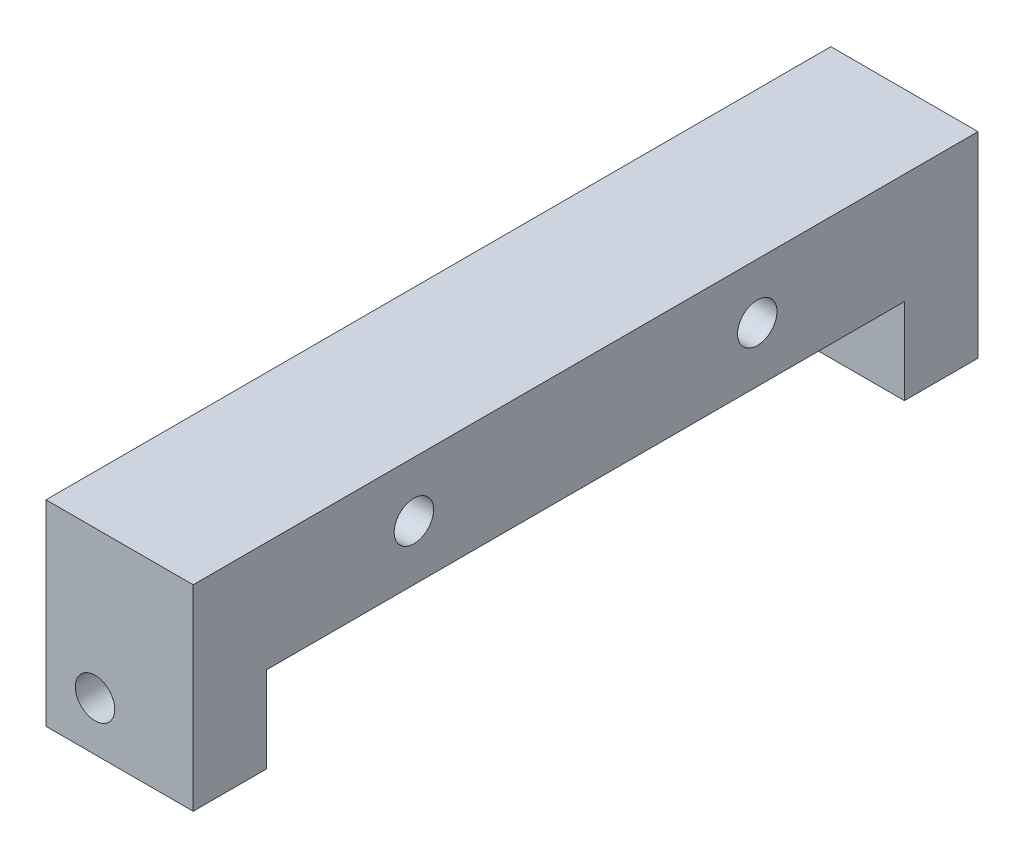
SolidWorks part; units mm, degrees
material "6061 Alloy"
ref_plane "Front Plane" through (0, 0, 0) normal (0, 0, 1) x (1, 0, 0)
ref_plane "Top Plane" through (0, 0, 0) normal (0, 1, 0) x (1, 0, 0)
ref_plane "Right Plane" through (0, 0, 0) normal (1, 0, 0) x (0, 0, -1)
sketch "Sketch1" plane through (0, 0, 0) normal (0, 0, 1) x (1, 0, 0)
  line L0 (9.525, 12.7) -> (-9.525, -12.7) construction
  line L1 (-9.525, 12.7) -> (9.525, 12.7)
  line L2 (-9.525, 12.7) -> (-9.525, -12.7)
  line L3 (-9.525, -12.7) -> (9.525, -12.7)
  line L4 (9.525, 12.7) -> (9.525, -12.7)
  dimension "D1" = 19.05
  dimension "D2" = 25.4
extrude "Extrude1" add sketch "Sketch1" along normal mid plane 101.6
sketch "Sketch2" plane through (9.525, 0, 0) normal (1, 0, 0) x (0, 0, -1)
  line L0 (-50.8, -12.7) -> (50.8, -12.7) construction
  line L1 (-41.275, -12.7) -> (41.275, -12.7)
  line L2 (-41.275, -12.7) -> (-41.275, -1.5875)
  line L3 (-41.275, -1.5875) -> (41.275, -1.5875)
  line L4 (41.275, -12.7) -> (41.275, -1.5875)
  line L5 (-50.8, -12.7) -> (-50.8, 12.7) construction
  line L6 (50.8, -12.7) -> (50.8, 12.7) construction
  dimension "D1" = 9.525
  dimension "D2" = 11.1125
  dimension "D3" = 9.525
extrude "Cut-Extrude1" cut sketch "Sketch2" against normal up to next
hole_wizard "1/4-20 Tapped Hole1" positions "Sketch4" profile "Sketch3" tap size "1/4-20" standard "Ansi Inch" end condition up to next
sketch "Sketch4" plane through (0, 0, -50.8) normal (0, 0, -1) x (-1, 0, 0)
  line L0 (9.525, -12.7) -> (-9.525, -12.7) construction
  line L1 (9.525, 12.7) -> (9.525, -12.7) construction
  point P0 (3.175, -6.35)
  dimension "D1" = 6.35
  dimension "D2" = 6.35
sketch "Sketch3" plane through (-3.175, -6.35, -50.8) normal (1, 0, 0) x (0, 1, 0)
  line L0 (0, 0) -> (0, 9.525)
  line L1 (0, 9.525) -> (2.5527, 9.525)
  line L2 (2.5527, 9.525) -> (2.5527, 0)
  line L5 (2.5527, 0) -> (0, 0)
  line L11 (0, -6.35) -> (0, 107.95) construction
  dimension "Thru Tap Drill Dia." = 5.1054
  dimension "Thru Tap Drill Depth" = 9.525
cosmetic thread "Hole Thread1" parameters "D2"=6.35
hole_wizard "1/4-20 Tapped Hole2" positions "Sketch6" profile "Sketch5" tap size "1/4-20" standard "Ansi Inch" end condition up to next
sketch "Sketch6" plane through (0, 0, 50.8) normal (0, 0, 1) x (1, 0, 0)
  point P0 (-3.175, -6.35)
sketch "Sketch5" plane through (-3.175, -6.35, 50.8) normal (1, 0, 0) x (0, -1, 0)
  line L0 (0, 0) -> (0, 9.525)
  line L1 (0, 9.525) -> (2.5527, 9.525)
  line L2 (2.5527, 9.525) -> (2.5527, 0)
  line L5 (2.5527, 0) -> (0, 0)
  line L11 (0, -6.35) -> (0, 107.95) construction
  dimension "Thru Tap Drill Dia." = 5.1054
  dimension "Thru Tap Drill Depth" = 9.525
cosmetic thread "Hole Thread2" parameters "D2"=6.35
hole_wizard "1/4-20 Tapped Hole3" positions "Sketch8" profile "Sketch7" tap size "1/4-20" standard "Ansi Inch"
sketch "Sketch8" plane through (0, -12.7, 0) normal (0, -1, 0) x (1, 0, 0)
  line L0 (-9.525, -50.8) -> (9.525, -50.8) construction
  line L1 (9.525, -41.275) -> (9.525, -50.8) construction
  line L2 (-9.525, 50.8) -> (9.525, 50.8) construction
  point P0 (4.7625, 46.0375)
  point P1 (4.7625, -46.0375)
  dimension "D1" = 4.7625
  dimension "D2" = 4.7625
  dimension "D3" = 4.7625
sketch "Sketch7" plane through (4.7625, -12.7, 46.0375) normal (1, 0, 0) x (0, 0, -1)
  line L0 (0, 0) -> (0, 18.0438)
  line L1 (0, 18.0438) -> (2.5527, 16.51)
  line L2 (2.5527, 16.51) -> (2.5527, 0)
  line L5 (2.5527, 0) -> (0, 0)
  line L10 (0, 18.0438) -> (-2.5527, 16.51) construction
  line L11 (0, -6.35) -> (0, 107.95) construction
  dimension "Tap Drill Dia." = 5.1054
  dimension "Tap Drill Depth" = 16.51
  dimension "Drill Angle" = 118
cosmetic thread "Hole Thread3" parameters "D1"=12.7, "D2"=6.35
cosmetic thread "Hole Thread4" parameters "D1"=12.7, "D2"=6.35
hole_wizard "1/4-20 Tapped Hole4" positions "Sketch10" profile "Sketch9" tap size "1/4-20" standard "Ansi Inch" end condition up to next
sketch "Sketch10" plane through (-9.525, 0, 0) normal (-1, 0, 0) x (0, 0, 1)
  line L0 (50.8, -12.7) -> (41.275, -12.7) construction
  line L1 (22.225, 5.5626) -> (-22.225, 5.5626) construction
  point P0 (-22.225, 5.5626)
  point P1 (22.225, 5.5626)
  point P9 (0, 5.5626)
  dimension "D1" = 18.2626
  dimension "D2" = 44.45
cosmetic thread "Hole Thread5" parameters "D2"=6.35
cosmetic thread "Hole Thread6" parameters "D2"=6.35
sketch "Sketch9" plane through (-9.525, 5.5626, -22.225) normal (0, 1, 0) x (0, 0, 1)
  line L0 (0, 0) -> (0, 19.05)
  line L1 (0, 19.05) -> (2.5527, 19.05)
  line L2 (2.5527, 19.05) -> (2.5527, 0)
  line L5 (2.5527, 0) -> (0, 0)
  line L11 (0, -6.35) -> (0, 107.95) construction
  dimension "Thru Tap Drill Dia." = 5.1054
  dimension "Thru Tap Drill Depth" = 19.05
